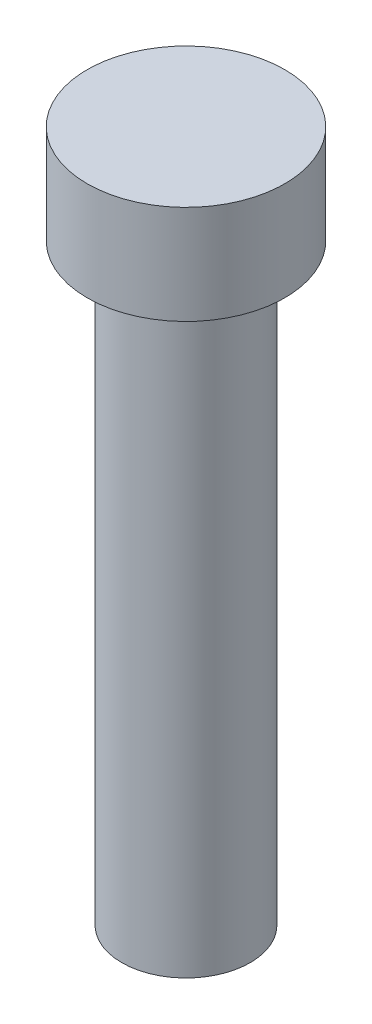
SolidWorks part; units mm, degrees
ref_plane "Front Plane" through (0, 0, 0) normal (0, 0, 1) x (1, 0, 0)
ref_plane "Top Plane" through (0, 0, 0) normal (0, 1, 0) x (1, 0, 0)
ref_plane "Right Plane" through (0, 0, 0) normal (1, 0, 0) x (0, 0, -1)
sketch "Sketch1" plane through (0, 0, 0) normal (0, 1, 0) x (1, 0, 0)
  circle A0 centre (0, 0) radius 3.25
  dimension "D1" = 6.5
extrude "Boss-Extrude1" add sketch "Sketch1" along normal blind 30
sketch "Sketch2" plane through (0, 30, 0) normal (0, 1, 0) x (1, 0, 0)
  circle A0 centre (0, 0) radius 5
  dimension "D1" = 10
extrude "Boss-Extrude2" add sketch "Sketch2" along normal blind 5
